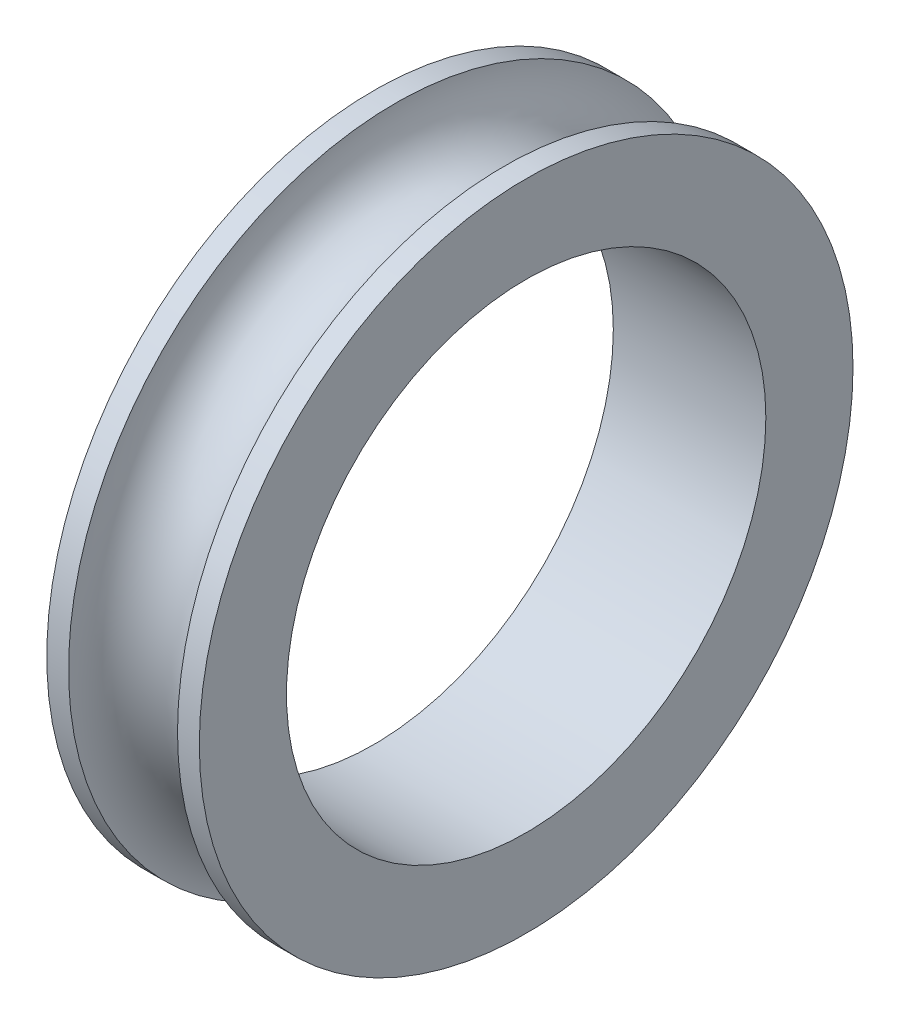
SolidWorks part; units mm, degrees
ref_plane "Plano frontal" through (0, 0, 0) normal (0, 0, 1) x (1, 0, 0)
ref_plane "Plano superior" through (0, 0, 0) normal (0, 1, 0) x (1, 0, 0)
ref_plane "Plano direito" through (0, 0, 0) normal (1, 0, 0) x (0, 0, -1)
sketch "Esboço1" plane through (0, 0, 0) normal (1, 0, 0) x (0, 0, -1)
  circle A0 centre (0, 0) radius 11
  circle A1 centre (0, 0) radius 15
  dimension "D1" = 22
  dimension "D2" = 30
extrude "Ressalto-extrusão1" add sketch "Esboço1" along normal blind 7
sketch "Esboço2" plane through (0, 0, 0) normal (0, 0, 1) x (1, 0, 0)
  line L0 (7, 15) -> (0, 15) construction
  circle A0 centre (3.5, 15) radius 2.5
  dimension "D1" = 5
ref_axis "Eixo1" through (7, 0, 0) along (-1, 0, 0)
revolve "Corte-Revolução1" cut sketch "Esboço2" angle 360 about axis through (7, 0, 0) along (-1, 0, 0)
